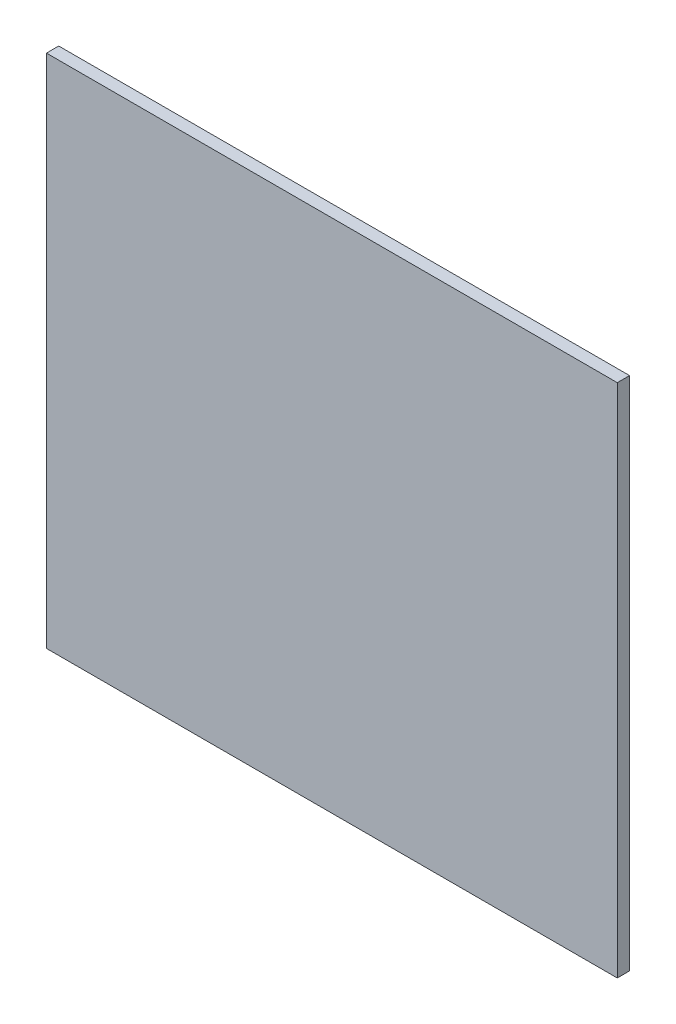
SolidWorks part; units mm, degrees
ref_plane "Front Plane" through (0, 0, 0) normal (0, 0, 1) x (1, 0, 0)
ref_plane "Top Plane" through (0, 0, 0) normal (0, 1, 0) x (1, 0, 0)
ref_plane "Right Plane" through (0, 0, 0) normal (1, 0, 0) x (0, 0, -1)
sketch "Sketch1" plane through (0, 0, 0) normal (0, 0, 1) x (1, 0, 0)
  line L0 (0, 12.8917) -> (0, -12.8917) construction
  line L1 (-46.5, 47.7877) -> (46.5, 47.7877)
  line L2 (-46.5, 47.7877) -> (-46.5, -36.2123)
  line L3 (-46.5, -36.2123) -> (46.5, -36.2123)
  line L4 (46.5, 47.7877) -> (46.5, -36.2123)
  line L5 (-26.5, 47.7877) -> (-41.5, 47.7877) construction
  point P4 (0, 47.7877)
  dimension "D1" = 93
  dimension "D2" = 84
extrude "Boss-Extrude1" add sketch "Sketch1" along normal blind 2
